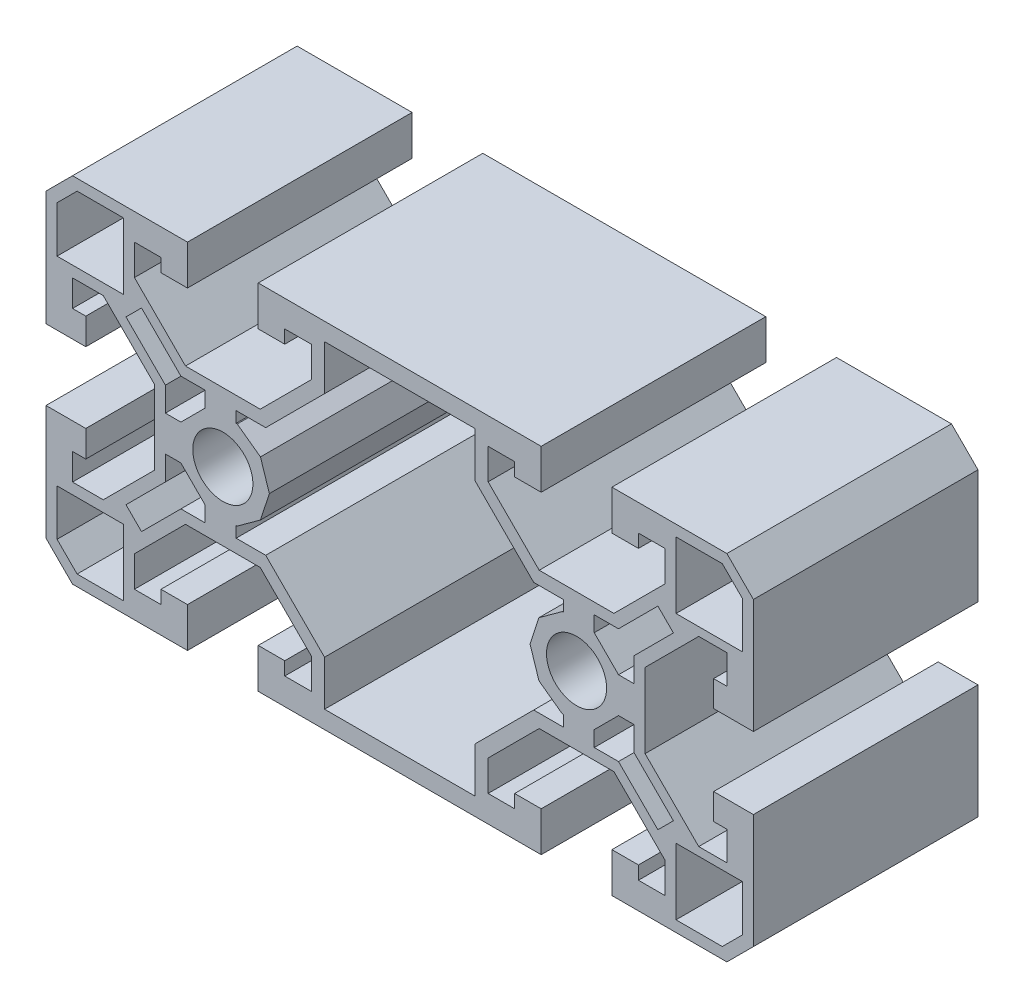
SolidWorks part; units mm, degrees
material "6061 Alloy"
ref_plane "Front" through (0, 0, 0) normal (0, 0, 1) x (1, 0, 0)
ref_plane "Top" through (0, 0, 0) normal (0, 1, 0) x (1, 0, 0)
ref_plane "Right" through (0, 0, 0) normal (1, 0, 0) x (0, 0, -1)
sketch "Sketch1" plane through (0, 0, 0) normal (0, 0, 1) x (1, 0, 0)
  line L0 (-367.3837, -5.1455) -> (-367.3837, -8.6205)
  line L1 (-367.3837, -8.6205) -> (-370.3837, -8.6205)
  line L2 (-373.1587, 0.6295) -> (-367.3837, -5.1455)
  line L3 (-370.3837, -8.6205) -> (-370.3837, -7.1205)
  line L4 (-381.6087, 0.6295) -> (-373.1587, 0.6295)
  line L5 (-370.3837, -7.1205) -> (-373.3837, -7.1205)
  line L6 (-387.3837, -5.1455) -> (-381.6087, 0.6295)
  line L7 (-373.3837, -7.1205) -> (-373.3837, -11.6205)
  line L8 (-387.3837, -8.6205) -> (-387.3837, -5.1455)
  line L9 (-373.3837, -11.6205) -> (-341.3837, -11.6205)
  line L10 (-384.3837, -8.6205) -> (-387.3837, -8.6205)
  line L11 (-341.3837, -11.6205) -> (-341.3837, -7.1205)
  line L12 (-384.3837, -7.1205) -> (-384.3837, -8.6205)
  line L13 (-341.3837, -7.1205) -> (-344.3837, -7.1205)
  line L14 (-381.3837, -7.1205) -> (-384.3837, -7.1205)
  line L15 (-344.3837, -7.1205) -> (-344.3837, -8.6205)
  line L16 (-381.3837, -11.6205) -> (-381.3837, -7.1205)
  line L17 (-344.3837, -8.6205) -> (-347.3837, -8.6205)
  line L18 (-394.3837, -11.6205) -> (-381.3837, -11.6205)
  line L19 (-347.3837, -8.6205) -> (-347.3837, -5.1455)
  line L20 (-397.3837, -8.6205) -> (-394.3837, -11.6205)
  line L21 (-347.3837, -5.1455) -> (-341.6087, 0.6295)
  line L22 (-397.3837, 4.3795) -> (-397.3837, -8.6205)
  line L23 (-341.6087, 0.6295) -> (-333.1587, 0.6295)
  line L24 (-392.8837, 4.3795) -> (-397.3837, 4.3795)
  line L25 (-333.1587, 0.6295) -> (-327.3837, -5.1455)
  line L26 (-392.8837, 1.3795) -> (-392.8837, 4.3795)
  line L27 (-327.3837, -5.1455) -> (-327.3837, -8.6205)
  line L28 (-394.3837, 1.3795) -> (-392.8837, 1.3795)
  line L29 (-327.3837, -8.6205) -> (-330.3837, -8.6205)
  line L30 (-394.3837, -1.6205) -> (-394.3837, 1.3795)
  line L31 (-330.3837, -8.6205) -> (-330.3837, -7.1205)
  line L32 (-390.9087, -1.6205) -> (-394.3837, -1.6205)
  line L33 (-330.3837, -7.1205) -> (-333.3837, -7.1205)
  line L34 (-385.1337, 4.1545) -> (-390.9087, -1.6205)
  line L35 (-333.3837, -7.1205) -> (-333.3837, -11.6205)
  line L36 (-385.1337, 12.6045) -> (-385.1337, 4.1545)
  line L37 (-333.3837, -11.6205) -> (-320.3837, -11.6205)
  line L38 (-390.9087, 18.3795) -> (-385.1337, 12.6045)
  line L39 (-320.3837, -11.6205) -> (-317.3837, -8.6205)
  line L40 (-394.3837, 18.3795) -> (-390.9087, 18.3795)
  line L41 (-317.3837, -8.6205) -> (-317.3837, 4.316)
  line L42 (-394.3837, 15.3795) -> (-394.3837, 18.3795)
  line L43 (-317.3837, 4.316) -> (-321.8837, 4.316)
  line L44 (-392.8837, 15.3795) -> (-394.3837, 15.3795)
  line L45 (-321.8837, 4.316) -> (-321.8837, 1.3795)
  line L46 (-392.8837, 12.3795) -> (-392.8837, 15.3795)
  line L47 (-321.8837, 1.3795) -> (-320.3837, 1.3795)
  line L48 (-397.3837, 12.3795) -> (-392.8837, 12.3795)
  line L49 (-320.3837, 1.3795) -> (-320.3837, -1.9126)
  line L50 (-397.3837, 25.3795) -> (-397.3837, 12.3795)
  line L51 (-320.3837, -1.9126) -> (-323.5666, -1.9126)
  line L52 (-394.3837, 28.3795) -> (-397.3837, 25.3795)
  line L53 (-323.5666, -1.9126) -> (-329.6337, 4.1545)
  line L54 (-381.3837, 28.3795) -> (-394.3837, 28.3795)
  line L55 (-329.6337, 4.1545) -> (-329.6337, 12.6045)
  line L56 (-381.3837, 23.8795) -> (-381.3837, 28.3795)
  line L57 (-329.6337, 12.6045) -> (-323.5666, 18.6716)
  line L58 (-384.3837, 23.8795) -> (-381.3837, 23.8795)
  line L59 (-323.5666, 18.6716) -> (-320.3837, 18.6716)
  line L60 (-384.3837, 25.3795) -> (-384.3837, 23.8795)
  line L61 (-320.3837, 18.6716) -> (-320.3837, 15.3795)
  line L62 (-387.3837, 25.3795) -> (-384.3837, 25.3795)
  line L63 (-320.3837, 15.3795) -> (-321.8837, 15.3795)
  line L64 (-387.3837, 21.9045) -> (-387.3837, 25.3795)
  line L65 (-321.8837, 15.3795) -> (-321.8837, 12.443)
  line L66 (-381.6087, 16.1295) -> (-387.3837, 21.9045)
  line L67 (-321.8837, 12.443) -> (-317.3837, 12.443)
  line L68 (-373.1587, 16.1295) -> (-381.6087, 16.1295)
  line L69 (-317.3837, 12.443) -> (-317.3837, 25.3795)
  line L70 (-367.3837, 21.9045) -> (-373.1587, 16.1295)
  line L71 (-317.3837, 25.3795) -> (-320.3837, 28.3795)
  line L72 (-367.3837, 25.3795) -> (-367.3837, 21.9045)
  line L73 (-320.3837, 28.3795) -> (-333.3837, 28.3795)
  line L74 (-370.3837, 25.3795) -> (-367.3837, 25.3795)
  line L75 (-333.3837, 28.3795) -> (-333.3837, 23.8795)
  line L76 (-370.3837, 23.8795) -> (-370.3837, 25.3795)
  line L77 (-333.3837, 23.8795) -> (-330.3837, 23.8795)
  line L78 (-373.3837, 23.8795) -> (-370.3837, 23.8795)
  line L79 (-330.3837, 23.8795) -> (-330.3837, 25.3795)
  line L80 (-373.3837, 28.3795) -> (-373.3837, 23.8795)
  line L81 (-330.3837, 25.3795) -> (-327.3837, 25.3795)
  line L82 (-341.3837, 28.3795) -> (-373.3837, 28.3795)
  line L83 (-327.3837, 25.3795) -> (-327.3837, 21.9045)
  line L84 (-341.3837, 23.8795) -> (-341.3837, 28.3795)
  line L85 (-327.3837, 21.9045) -> (-333.1587, 16.1295)
  line L86 (-344.3837, 23.8795) -> (-341.3837, 23.8795)
  line L87 (-333.1587, 16.1295) -> (-341.6087, 16.1295)
  line L88 (-344.3837, 25.3795) -> (-344.3837, 23.8795)
  line L89 (-341.6087, 16.1295) -> (-347.3837, 21.9045)
  line L90 (-347.3837, 25.3795) -> (-344.3837, 25.3795)
  line L91 (-347.3837, 21.9045) -> (-347.3837, 25.3795)
  line L92 (-373.1304, 11.4696) -> (-372.1264, 8.3795)
  line L93 (-372.1264, 8.3795) -> (-373.1304, 5.2893)
  line L94 (-375.7591, 13.3795) -> (-373.1304, 11.4696)
  line L95 (-373.1304, 5.2893) -> (-375.7591, 3.3795)
  line L96 (-375.8837, 13.3795) -> (-375.7591, 13.3795)
  line L97 (-375.7591, 3.3795) -> (-375.8837, 3.3795)
  line L98 (-375.8837, 14.6295) -> (-375.8837, 13.3795)
  line L99 (-375.8837, 3.3795) -> (-375.8837, 2.1295)
  line L100 (-372.5373, 14.6295) -> (-375.8837, 14.6295)
  line L101 (-375.8837, 2.1295) -> (-372.5373, 2.1295)
  line L102 (-365.8837, 21.2831) -> (-372.5373, 14.6295)
  line L103 (-372.5373, 2.1295) -> (-365.8837, -4.5242)
  line L104 (-365.8837, 26.3795) -> (-365.8837, 21.2831)
  line L105 (-365.8837, -4.5242) -> (-365.8837, -9.6205)
  line L106 (-348.8837, 26.3795) -> (-365.8837, 26.3795)
  line L107 (-365.8837, -9.6205) -> (-348.8837, -9.6205)
  line L108 (-348.8837, 21.2831) -> (-348.8837, 26.3795)
  line L109 (-348.8837, -9.6205) -> (-348.8837, -4.5242)
  line L110 (-342.23, 14.6295) -> (-348.8837, 21.2831)
  line L111 (-348.8837, -4.5242) -> (-342.23, 2.1295)
  line L112 (-338.8837, 14.6295) -> (-342.23, 14.6295)
  line L113 (-342.23, 2.1295) -> (-338.8837, 2.1295)
  line L114 (-338.8837, 13.3795) -> (-338.8837, 14.6295)
  line L115 (-338.8837, 2.1295) -> (-338.8837, 3.3795)
  line L116 (-339.0083, 13.3795) -> (-338.8837, 13.3795)
  line L117 (-338.8837, 3.3795) -> (-339.0083, 3.3795)
  line L118 (-341.6369, 11.4696) -> (-339.0083, 13.3795)
  line L119 (-339.0083, 3.3795) -> (-341.6369, 5.2893)
  line L120 (-342.641, 8.3795) -> (-341.6369, 11.4696)
  line L121 (-341.6369, 5.2893) -> (-342.641, 8.3795)
  line L122 (-382.1264, 14.8795) -> (-386.5813, 19.3344)
  line L123 (-386.5813, 19.3344) -> (-388.3386, 17.5771)
  line L124 (-379.3837, 14.8795) -> (-382.1264, 14.8795)
  line L125 (-388.3386, 17.5771) -> (-383.8837, 13.1222)
  line L126 (-379.3837, 13.1253) -> (-379.3837, 14.8795)
  line L127 (-383.8837, 13.1222) -> (-383.8837, 10.3795)
  line L128 (-382.1295, 10.3795) -> (-379.3837, 13.1253)
  line L129 (-383.8837, 10.3795) -> (-382.1295, 10.3795)
  line L130 (-332.6409, 1.8795) -> (-328.186, -2.5754)
  line L131 (-328.186, -2.5754) -> (-326.4288, -0.8182)
  line L132 (-335.3837, 1.8795) -> (-332.6409, 1.8795)
  line L133 (-326.4288, -0.8182) -> (-330.8837, 3.6367)
  line L134 (-335.3837, 3.6337) -> (-335.3837, 1.8795)
  line L135 (-330.8837, 3.6367) -> (-330.8837, 6.3795)
  line L136 (-332.6379, 6.3795) -> (-335.3837, 3.6337)
  line L137 (-330.8837, 6.3795) -> (-332.6379, 6.3795)
  line L138 (-383.8837, 3.6367) -> (-388.3386, -0.8182)
  line L139 (-388.3386, -0.8182) -> (-386.5813, -2.5754)
  line L140 (-383.8837, 6.3795) -> (-383.8837, 3.6367)
  line L141 (-386.5813, -2.5754) -> (-382.1264, 1.8795)
  line L142 (-382.1295, 6.3795) -> (-383.8837, 6.3795)
  line L143 (-382.1264, 1.8795) -> (-379.3837, 1.8795)
  line L144 (-379.3837, 3.6337) -> (-382.1295, 6.3795)
  line L145 (-379.3837, 1.8795) -> (-379.3837, 3.6337)
  line L146 (-330.8837, 13.1222) -> (-326.4288, 17.5771)
  line L147 (-326.4288, 17.5771) -> (-328.186, 19.3344)
  line L148 (-330.8837, 10.3795) -> (-330.8837, 13.1222)
  line L149 (-328.186, 19.3344) -> (-332.6409, 14.8795)
  line L150 (-332.6379, 10.3795) -> (-330.8837, 10.3795)
  line L151 (-332.6409, 14.8795) -> (-335.3837, 14.8795)
  line L152 (-335.3837, 13.1253) -> (-332.6379, 10.3795)
  line L153 (-335.3837, 14.8795) -> (-335.3837, 13.1253)
  line L154 (-393.8659, 27.1295) -> (-396.1337, 24.8617)
  line L155 (-396.1337, 24.8617) -> (-396.1337, 19.6295)
  line L156 (-388.6337, 27.1295) -> (-393.8659, 27.1295)
  line L157 (-396.1337, 19.6295) -> (-388.6337, 19.6295)
  line L158 (-388.6337, 19.6295) -> (-388.6337, 27.1295)
  line L159 (-320.9014, -10.3705) -> (-318.6337, -8.1028)
  line L160 (-318.6337, -8.1028) -> (-318.6337, -2.8705)
  line L161 (-326.1337, -10.3705) -> (-320.9014, -10.3705)
  line L162 (-318.6337, -2.8705) -> (-326.1337, -2.8705)
  line L163 (-326.1337, -2.8705) -> (-326.1337, -10.3705)
  line L164 (-396.1337, -2.8705) -> (-396.1337, -8.1028)
  line L165 (-396.1337, -8.1028) -> (-393.8659, -10.3705)
  line L166 (-388.6337, -2.8705) -> (-396.1337, -2.8705)
  line L167 (-393.8659, -10.3705) -> (-388.6337, -10.3705)
  line L168 (-388.6337, -10.3705) -> (-388.6337, -2.8705)
  line L169 (-318.6337, 19.6295) -> (-318.6337, 24.8617)
  line L170 (-318.6337, 24.8617) -> (-320.9014, 27.1295)
  line L171 (-326.1337, 19.6295) -> (-318.6337, 19.6295)
  line L172 (-320.9014, 27.1295) -> (-326.1337, 27.1295)
  line L173 (-326.1337, 27.1295) -> (-326.1337, 19.6295)
  circle A0 centre (-337.3837, 8.3795) radius 3.4
  circle A1 centre (-377.3837, 8.3795) radius 3.4
extrude "Extrude1" add sketch "Sketch1" along normal blind 25.4
